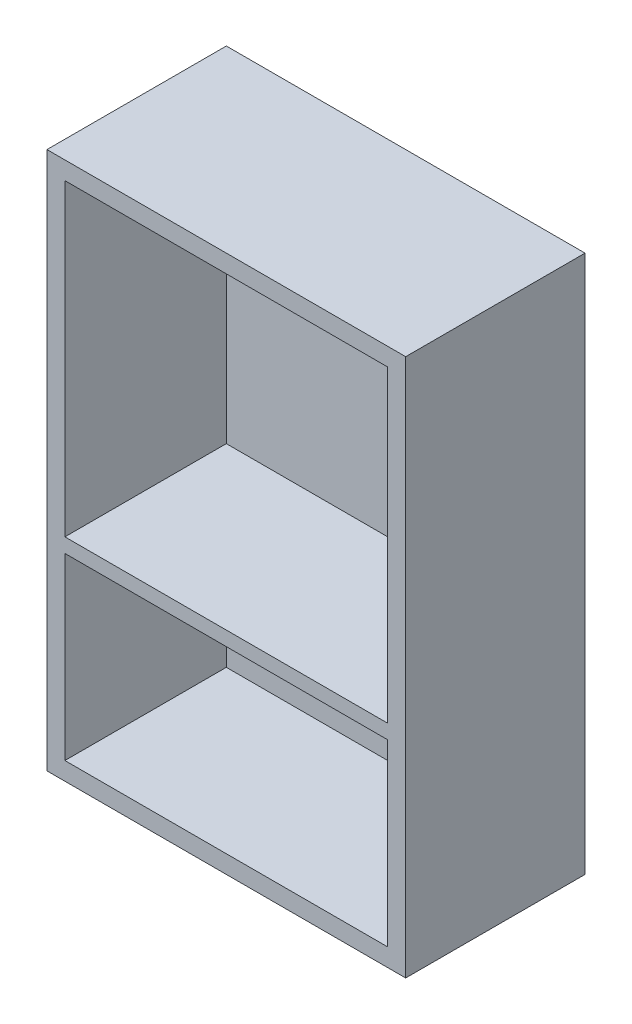
SolidWorks part; units mm, degrees
ref_plane "Front Plane" through (0, 0, 0) normal (0, 0, 1) x (1, 0, 0)
ref_plane "Top Plane" through (0, 0, 0) normal (0, 1, 0) x (1, 0, 0)
ref_plane "Right Plane" through (0, 0, 0) normal (1, 0, 0) x (0, 0, -1)
sketch "Sketch1" plane through (0, 0, 0) normal (0, 0, 1) x (1, 0, 0)
  line L1 (-50, 75) -> (50, 75)
  line L2 (-50, 75) -> (-50, -75)
  line L3 (-50, -75) -> (50, -75)
  line L4 (50, 75) -> (50, -75)
  line L5 (-50, 75) -> (50, -75) construction
  line L6 (-50, -75) -> (50, 75) construction
  point P0 (0, 0)
  dimension "D1" = 150
  dimension "D2" = 100
extrude "Boss-Extrude1" add sketch "Sketch1" along normal blind 5
sketch "Sketch2" plane through (0, 0, 5) normal (0, 0, 1) x (1, 0, 0)
  line L0 (-50, -75) -> (50, -75) construction
  line L1 (-50, -75) -> (50, -75)
  line L2 (-50, -75) -> (-50, 75)
  line L3 (-50, 75) -> (50, 75)
  line L4 (50, -75) -> (50, 75)
  line L5 (-50, -75) -> (50, 75) construction
  line L6 (-50, 75) -> (50, -75) construction
  line L7 (-45, 70) -> (45, 70)
  line L8 (-45, 70) -> (-45, -16)
  line L9 (-45, -16) -> (45, -16)
  line L10 (45, 70) -> (45, -16)
  line L11 (-45, 70) -> (45, -16) construction
  line L12 (-45, -16) -> (45, 70) construction
  line L13 (-45, -70) -> (45, -70)
  line L14 (-45, -70) -> (-45, -20)
  line L15 (-45, -20) -> (45, -20)
  line L16 (45, -70) -> (45, -20)
  line L17 (-45, -70) -> (45, -20) construction
  line L18 (-45, -20) -> (45, -70) construction
  line L19 (-50, 75) -> (-50, -75) construction
  point P0 (0, 0)
  point P6 (0, 27)
  point P11 (0, -45)
  dimension "D1" = 5
  dimension "D2" = 0
  dimension "D3" = 0
  dimension "D4" = 5
  dimension "D5" = 5
  dimension "D6" = 5
  dimension "D7" = 5
  dimension "D8" = 5
  dimension "D9" = 4
  dimension "D10" = 50
extrude "Boss-Extrude2" add sketch "Sketch2" along normal blind 45
